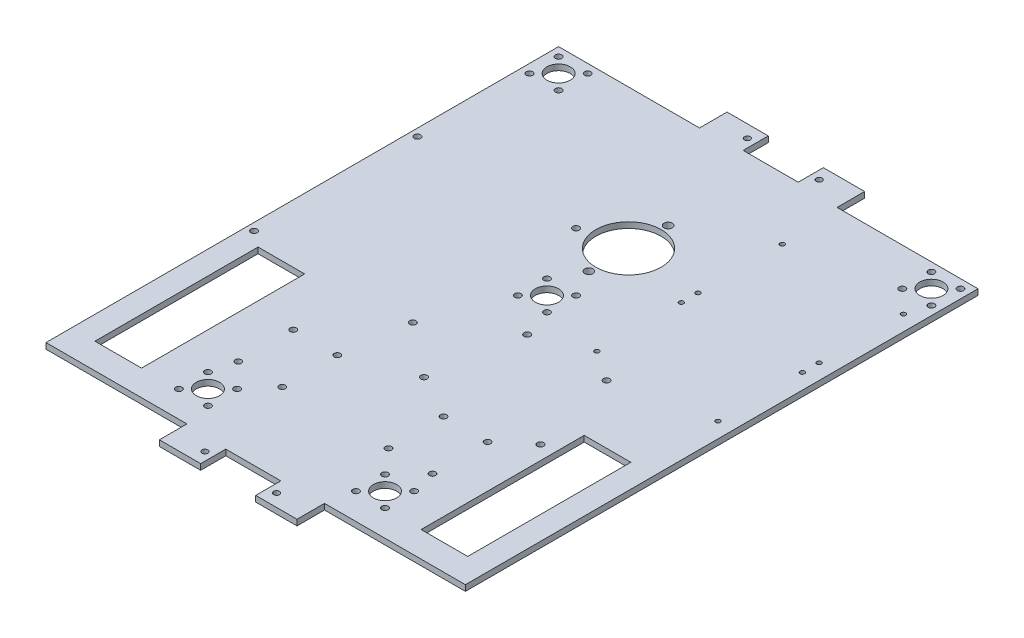
SolidWorks part; units mm, degrees
ref_plane "Front Plane" through (0, 0, 0) normal (0, 0, 1) x (1, 0, 0)
ref_plane "Top Plane" through (0, 0, 0) normal (0, 1, 0) x (1, 0, 0)
ref_plane "Right Plane" through (0, 0, 0) normal (1, 0, 0) x (0, 0, -1)
sketch "Sketch1" plane through (0, 0, 0) normal (0, 1, 0) x (1, 0, 0)
  line L0 (114.3, 279.4) -> (114.3, 0) construction
  line L1 (0, 0) -> (228.6, 0)
  line L2 (0, 0) -> (0, 279.4)
  line L3 (0, 279.4) -> (228.6, 279.4)
  line L4 (228.6, 0) -> (228.6, 279.4)
  line L5 (0, 50.8) -> (228.6, 50.8) construction
  line L6 (0, 190.5) -> (228.6, 190.5) construction
  dimension "D1" = 228.6
  dimension "D2" = 279.4
  dimension "D3" = 50.8
  dimension "D4" = 139.7
extrude "Boss-Extrude1" add sketch "Sketch1" along normal blind 3.175
sketch "Sketch3" plane through (0, 3.175, 0) normal (0, 1, 0) x (1, 0, 0)
  line L0 (114.3, 279.4) -> (114.3, 0) construction
  line L1 (228.6, 279.4) -> (0, 279.4) construction
  line L2 (0, 0) -> (228.6, 0) construction
  line L3 (0, 58.42) -> (228.6, 58.42) construction
  line L4 (0, 279.4) -> (0, 0) construction
  line L5 (228.6, 0) -> (228.6, 279.4) construction
  line L6 (215.9, 13.97) -> (190.5, 13.97)
  line L7 (12.7, 13.97) -> (38.1, 13.97)
  line L8 (12.7, 13.97) -> (12.7, 102.87)
  line L9 (12.7, 102.87) -> (38.1, 102.87)
  line L10 (38.1, 13.97) -> (38.1, 102.87)
  line L11 (12.7, 13.97) -> (38.1, 102.87) construction
  line L12 (12.7, 102.87) -> (38.1, 13.97) construction
  line L13 (53.34, 38.42) -> (93.34, 38.42) construction
  line L14 (53.34, 38.42) -> (53.34, 78.42) construction
  line L15 (53.34, 78.42) -> (93.34, 78.42) construction
  line L16 (93.34, 38.42) -> (93.34, 78.42) construction
  line L17 (53.34, 38.42) -> (93.34, 78.42) construction
  line L18 (53.34, 78.42) -> (93.34, 38.42) construction
  line L19 (190.5, 13.97) -> (190.5, 102.87)
  line L20 (215.9, 13.97) -> (215.9, 102.87)
  line L21 (215.9, 102.87) -> (190.5, 102.87)
  circle A0 centre (85.34, 43.42) radius 1.7
  circle A1 centre (61.34, 43.42) radius 1.7
  circle A2 centre (85.34, 73.42) radius 1.7
  circle A3 centre (61.34, 73.42) radius 1.7
  circle A4 centre (167.26, 73.42) radius 1.7
  circle A5 centre (143.26, 73.42) radius 1.7
  circle A6 centre (167.26, 43.42) radius 1.7
  circle A7 centre (143.26, 43.42) radius 1.7
  point P32 (25.4, 58.42)
  point P37 (73.34, 58.42)
  dimension "D1" = 3.4
  dimension "D2" = 3.4
  dimension "D3" = 3.4
  dimension "D4" = 3.4
  dimension "D5" = 15
  dimension "D6" = 25.4
  dimension "D7" = 88.9
  dimension "D8" = 40
  dimension "D9" = 40
  dimension "D10" = 8
  dimension "6" = 27.94
extrude "Cut-Extrude1" cut sketch "Sketch3" against normal through all
sketch "Sketch4" plane through (0, 3.175, 0) normal (0, 1, 0) x (1, 0, 0)
  circle A0 centre (114.3, 203.2) radius 17.78
  circle A1 centre (114.3, 224.79) radius 2.25
  circle A2 centre (114.3, 181.61) radius 2.25
extrude "Cut-Extrude2" cut sketch "Sketch4" against normal through all
sketch "Sketch5" plane through (0, 3.175, 0) normal (0, 1, 0) x (1, 0, 0)
  circle A0 centre (90.5, 198.41) radius 1.75
  circle A1 centre (90.5, 109.41) radius 1.75
  circle A2 centre (4, 109.41) radius 1.75
  circle A3 centre (4, 198.41) radius 1.75
extrude "Cut-Extrude3" cut sketch "Sketch5" against normal through all
sketch "Sketch6" plane through (0, 3.175, 0) normal (0, 1, 0) x (1, 0, 0)
  circle A0 centre (154.25, 247.1021) radius 1.25
  circle A1 centre (220.25, 247.1021) radius 1.25
  circle A2 centre (220.25, 201.1021) radius 1.25
  circle A3 centre (154.25, 201.1021) radius 1.25
  circle A4 centre (220.25, 192.0221) radius 1.25
  circle A5 centre (220.25, 146.0221) radius 1.25
  circle A6 centre (154.25, 146.0221) radius 1.25
  circle A7 centre (154.25, 192.0221) radius 1.25
extrude "Cut-Extrude4" cut sketch "Sketch6" against normal through all
sketch "Sketch7" plane through (0, 3.175, 0) normal (0, 1, 0) x (1, 0, 0)
  circle A0 centre (127.38, 134.915) radius 1.75
  circle A1 centre (170.62, 134.915) radius 1.75
  circle A2 centre (119.38, 86.675) radius 1.75
  circle A3 centre (182.82, 86.675) radius 1.75
extrude "Cut-Extrude5" cut sketch "Sketch7" against normal through all
sketch "Sketch8" plane through (0, 3.175, 0) normal (0, 1, 0) x (1, 0, 0)
  circle A0 centre (20.6375, 258.7625) radius 1.727 construction
  circle A1 centre (4.7625, 258.7625) radius 1.727 construction
  circle A2 centre (4.7625, 274.6375) radius 1.727 construction
  circle A3 centre (20.6375, 274.6375) radius 1.727 construction
  circle A4 centre (12.7, 266.7) radius 6.35 construction
  circle A5 centre (20.6375, 258.7625) radius 1.727
  circle A6 centre (4.7625, 258.7625) radius 1.727
  circle A7 centre (4.7625, 274.6375) radius 1.727
  circle A8 centre (20.6375, 274.6375) radius 1.727
  circle A9 centre (12.7, 266.7) radius 6.35
  circle A10 centre (58.1025, 14.2875) radius 1.727 construction
  circle A11 centre (73.9775, 14.2875) radius 1.727 construction
  circle A12 centre (66.04, 22.225) radius 6.35 construction
  circle A13 centre (58.1025, 30.1625) radius 1.727 construction
  circle A14 centre (73.9775, 30.1625) radius 1.727 construction
  circle A15 centre (58.1025, 14.2875) radius 1.727
  circle A16 centre (73.9775, 14.2875) radius 1.727
  circle A17 centre (66.04, 22.225) radius 6.35
  circle A18 centre (58.1025, 30.1625) radius 1.727
  circle A19 centre (73.9775, 30.1625) radius 1.727
  circle A20 centre (170.4975, 14.2875) radius 1.727 construction
  circle A21 centre (154.6225, 14.2875) radius 1.727 construction
  circle A22 centre (154.6225, 30.1625) radius 1.727 construction
  circle A23 centre (170.4975, 30.1625) radius 1.727 construction
  circle A24 centre (162.56, 22.225) radius 6.35 construction
  circle A25 centre (170.4975, 14.2875) radius 1.727
  circle A26 centre (154.6225, 14.2875) radius 1.727
  circle A27 centre (154.6225, 30.1625) radius 1.727
  circle A28 centre (170.4975, 30.1625) radius 1.727
  circle A29 centre (162.56, 22.225) radius 6.35
  circle A30 centre (106.3625, 150.8125) radius 1.727 construction
  circle A31 centre (122.2375, 150.8125) radius 1.727 construction
  circle A32 centre (114.3, 158.75) radius 6.35 construction
  circle A33 centre (106.3625, 166.6875) radius 1.727 construction
  circle A34 centre (122.2375, 166.6875) radius 1.727 construction
  circle A35 centre (106.3625, 150.8125) radius 1.727
  circle A36 centre (122.2375, 150.8125) radius 1.727
  circle A37 centre (114.3, 158.75) radius 6.35
  circle A38 centre (106.3625, 166.6875) radius 1.727
  circle A39 centre (122.2375, 166.6875) radius 1.727
  circle A40 centre (223.8375, 258.7625) radius 1.727 construction
  circle A41 centre (207.9625, 258.7625) radius 1.727 construction
  circle A42 centre (207.9625, 274.6375) radius 1.727 construction
  circle A43 centre (223.8375, 274.6375) radius 1.727 construction
  circle A44 centre (215.9, 266.7) radius 6.35 construction
  circle A45 centre (223.8375, 258.7625) radius 1.727
  circle A46 centre (207.9625, 258.7625) radius 1.727
  circle A47 centre (207.9625, 274.6375) radius 1.727
  circle A48 centre (223.8375, 274.6375) radius 1.727
  circle A49 centre (215.9, 266.7) radius 6.35
extrude "Cut-Extrude6" cut sketch "Sketch8" against normal through all both
sketch "Sketch10" plane through (0, 0, 0) normal (0, -1, 0) x (1, 0, 0)
  line L0 (0, 0) -> (228.6, 0) construction
  line L1 (76.8, 15) -> (151.8, 15)
  line L2 (76.8, 15) -> (76.8, 0)
  line L3 (76.8, 0) -> (151.8, 0)
  line L4 (151.8, 15) -> (151.8, 0)
  line L5 (76.8, 15) -> (151.8, 0) construction
  line L6 (76.8, 0) -> (151.8, 15) construction
  line L7 (0, -139.7) -> (228.6, -139.7) construction
  line L8 (0, -279.4) -> (0, 0) construction
  line L9 (228.6, 0) -> (228.6, -279.4) construction
  line L10 (76.8, -279.4) -> (151.8, -294.4) construction
  line L11 (76.8, -294.4) -> (151.8, -279.4) construction
  line L12 (151.8, -294.4) -> (151.8, -279.4)
  line L13 (76.8, -279.4) -> (151.8, -279.4)
  line L14 (76.8, -294.4) -> (76.8, -279.4)
  line L15 (76.8, -294.4) -> (151.8, -294.4)
  point P0 (114.3, 7.5)
  point P7 (114.3, 0)
  point P18 (114.3, -286.9)
  dimension "D1" = 15
  dimension "D2" = 75
extrude "Boss-Extrude2" add sketch "Sketch10" against normal up to surface (3.175 mm away) up to face at (154.6225, 3.175, -28.4355)
sketch "Sketch9" plane through (0, 3.175, 0) normal (0, 1, 0) x (1, 0, 0)
  line L1 (99.3, 280.7) -> (129.3, 280.7)
  line L2 (99.3, 280.7) -> (99.3, 294.4)
  line L3 (99.3, 294.4) -> (129.3, 294.4)
  line L4 (137.3, 280.7) -> (137.3, 294.4)
  line L5 (137.3, 294.4) -> (91.3, 294.4)
  line L6 (91.3, 294.4) -> (91.3, 280.7)
  line L7 (91.3, 280.7) -> (137.3, 280.7)
  line L8 (137.3, 280.7) -> (137.3, 294.4) construction
  line L9 (137.3, 294.4) -> (91.3, 294.4) construction
  line L10 (91.3, 294.4) -> (91.3, 280.7) construction
  line L11 (91.3, 280.7) -> (137.3, 280.7) construction
  line L12 (137.3, -15) -> (137.3, -1.3)
  line L13 (137.3, -1.3) -> (91.3, -1.3)
  line L14 (91.3, -1.3) -> (91.3, -15)
  line L15 (91.3, -15) -> (137.3, -15)
  line L16 (137.3, -15) -> (137.3, -1.3) construction
  line L17 (137.3, -1.3) -> (91.3, -1.3) construction
  line L18 (91.3, -1.3) -> (91.3, -15) construction
  line L19 (91.3, -15) -> (137.3, -15) construction
  line L20 (129.3, 280.7) -> (129.3, 294.4)
  line L21 (99.3, 280.7) -> (129.3, 294.4) construction
  line L22 (99.3, 294.4) -> (129.3, 280.7) construction
  line L23 (99.3, -15) -> (129.3, -15)
  line L24 (99.3, -15) -> (99.3, -1.3)
  line L25 (99.3, -1.3) -> (129.3, -1.3)
  line L26 (129.3, -15) -> (129.3, -1.3)
  line L27 (99.3, -15) -> (129.3, -1.3) construction
  line L28 (99.3, -1.3) -> (129.3, -15) construction
  circle A0 centre (133.85, 287.55) radius 1.6 construction
  circle A1 centre (94.75, 287.55) radius 1.6 construction
  circle A2 centre (133.85, 287.55) radius 1.6
  circle A3 centre (94.75, 287.55) radius 1.6
  circle A5 centre (133.85, -8.15) radius 1.6
  circle A6 centre (133.85, -8.15) radius 1.6
  circle A7 centre (94.75, -8.15) radius 1.6
  circle A8 centre (94.75, -8.15) radius 1.6
  point P18 (114.3, 287.55)
  point P25 (114.3, -1.3)
  point P26 (114.3, 280.7)
  point P27 (114.3, -8.15)
  dimension "D5" = 30
  dimension "D1" = 0
  dimension "D2" = 0
  dimension "D3" = 0
  dimension "D4" = 0
extrude "Cut-Extrude7" cut sketch "Sketch9" against normal through all both
equation "\"D5@Sketch9\"=30mm"
equation "\"D2@Sketch10\"=75mm"
equation "\"D1@Sketch10\"=15mm"
